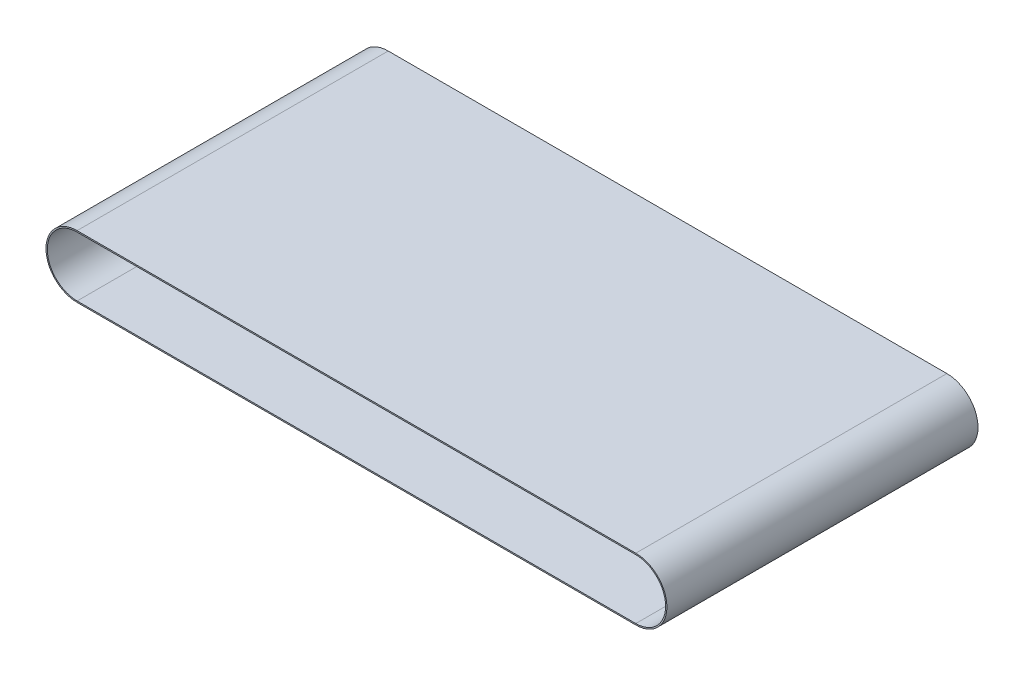
SolidWorks part; units mm, degrees
ref_plane "Plan de face" through (0, 0, 0) normal (0, 0, 1) x (1, 0, 0)
ref_plane "Plan de dessus" through (0, 0, 0) normal (0, 1, 0) x (1, 0, 0)
ref_plane "Plan de droite" through (0, 0, 0) normal (1, 0, 0) x (0, 0, -1)
sketch "Sketch2" plane through (0, 0, 0) normal (0, 0, 1) x (1, 0, 0)
  circle A0 centre (0, 0) radius 12.5
  circle A1 centre (0, 0) radius 4
  circle A2 centre (30, 0) radius 4
  circle A3 centre (30, 0) radius 12.5
  circle A4 centre (60, 0) radius 4
  circle A5 centre (60, 0) radius 12.5
  circle A6 centre (90, 0) radius 4
  circle A7 centre (90, 0) radius 12.5
  circle A8 centre (120, 0) radius 4
  circle A9 centre (120, 0) radius 12.5
  circle A10 centre (150, 0) radius 4
  circle A11 centre (150, 0) radius 12.5
  circle A12 centre (180, 0) radius 4
  circle A13 centre (180, 0) radius 12.5
  circle A14 centre (210, 0) radius 4
  circle A15 centre (210, 0) radius 12.5
  dimension "D1" = 25
  dimension "D2" = 8
ref_plane "Plane1" through (0, 0, 60) normal (0, 0, 1) x (1, 0, 0)
sketch "Sketch3" plane through (0, 0, 60) normal (0, 0, 1) x (1, 0, 0)
  line L0 (-2.75, 0) -> (212.75, 0) construction
  line L1 (-2.75, 12) -> (212.75, 12)
  line L2 (-2.75, -12) -> (212.75, -12)
  line L3 (-2.75, 11.5) -> (212.75, 11.5)
  line L4 (-2.75, -11.5) -> (212.75, -11.5)
  arc A0 (-2.75, 12) -> (-2.75, -12) centre (-2.75, 0) ccw
  arc A1 (212.75, -12) -> (212.75, 12) centre (212.75, 0) ccw
  arc A2 (212.75, -11.5) -> (212.75, 11.5) centre (212.75, 0) ccw
  arc A3 (-2.75, 11.5) -> (-2.75, -11.5) centre (-2.75, 0) ccw
  point P3 (105, 0)
  dimension "D3" = 2.75
  dimension "D1" = 24
  dimension "D2" = 2.75
  dimension "D4" = 0.5
extrude "Boss-Extrude1" add sketch "Sketch3" against normal blind 120
